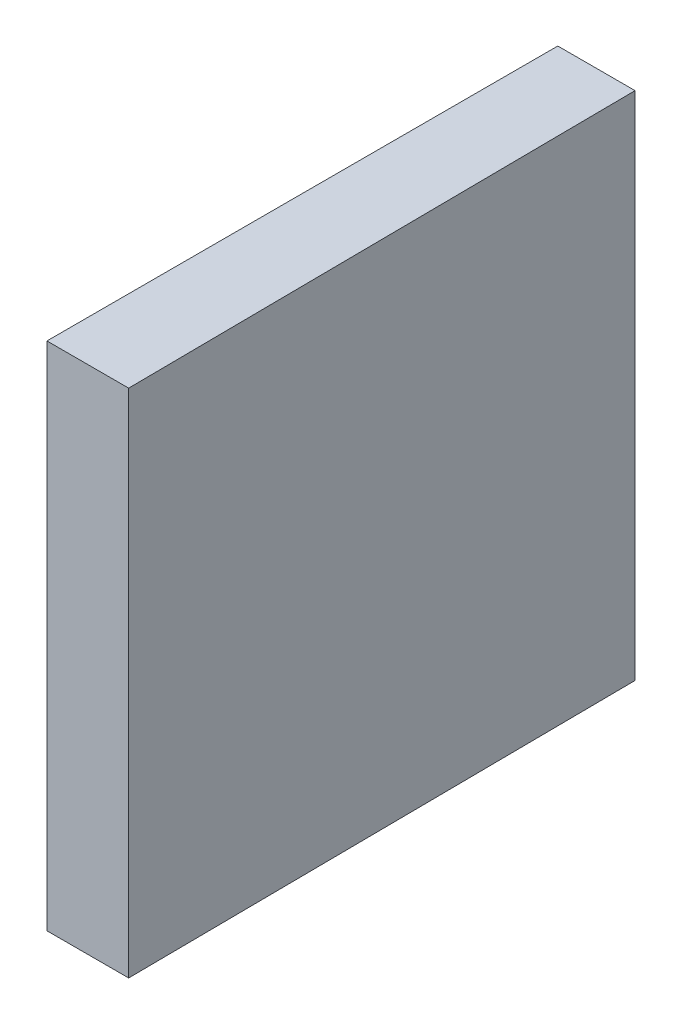
SolidWorks part; units mm, degrees
ref_plane "前视基准面" through (0, 0, 0) normal (0, 0, 1) x (1, 0, 0)
ref_plane "上视基准面" through (0, 0, 0) normal (0, 1, 0) x (1, 0, 0)
ref_plane "右视基准面" through (0, 0, 0) normal (1, 0, 0) x (0, 0, -1)
sketch "草图1" plane through (0, 0, 0) normal (0, 1, 0) x (1, 0, 0)
  line L0 (-12.1202, 0) -> (19.0875, 0) construction
  line L1 (0, 25) -> (0, -25)
  line L2 (0, -25) -> (8, -25)
  line L3 (8, -25) -> (7.5637, 25)
  line L4 (0, 25) -> (7.5637, 25)
  point P5 (0, 0)
  dimension "D1" = 8
  dimension "D2" = 50
  dimension "D3" = 0.5
extrude "凸台-拉伸1" add sketch "草图1" along normal blind 50
